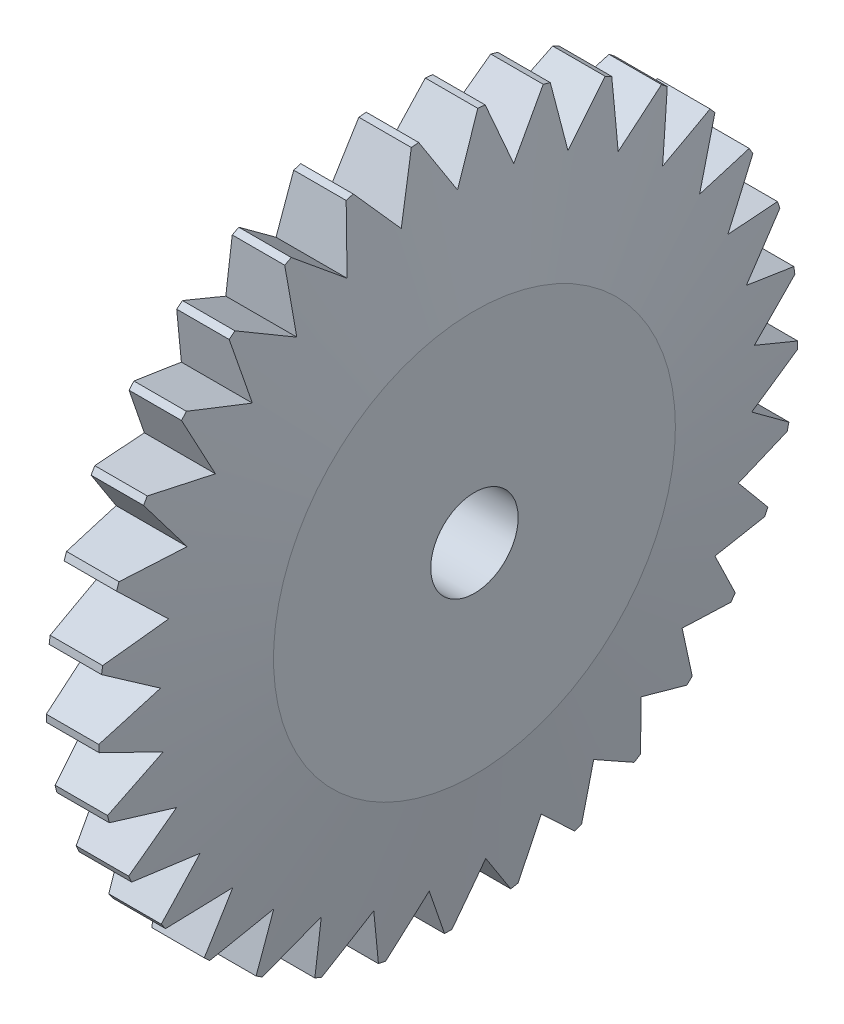
SolidWorks part; units mm, degrees
ref_plane "Front Plane" through (0, 0, 0) normal (0, 0, 1) x (1, 0, 0)
ref_plane "Top Plane" through (0, 0, 0) normal (0, 1, 0) x (1, 0, 0)
ref_plane "Right Plane" through (0, 0, 0) normal (1, 0, 0) x (0, 0, -1)
sketch "Sketch1" plane through (0, 0, 0) normal (1, 0, 0) x (0, 0, -1)
  circle A0 centre (0, 0) radius 40
  circle A1 centre (0, 0) radius 5
  dimension "D1" = 80
  dimension "D2" = 10
extrude "Boss-Extrude1" add sketch "Sketch1" along normal mid plane 12
sketch "Sketch2" plane through (6, 0, 0) normal (1, 0, 0) x (0, 0, -1)
  line L0 (0, 1.033) -> (0, 49.8392) construction
  line L1 (0, 40) -> (0, 34)
  line L2 (0, 34) -> (3.3814, 39.8568)
  line L4 (-3.3814, 39.8568) -> (0, 34)
  circle A0 centre (0, 0) radius 40 construction
  arc A1 (-3.3814, 39.8568) -> (3.3814, 39.8568) centre (0, 34) cw
  dimension "D1" = 30
  dimension "D2" = 30
  dimension "D3" = 6
chamfer "Chamfer2" distance 3 angle 80 1 edges at (6, 0, -40)
chamfer "Chamfer3" distance 3 angle 80 1 edges at (-6, 0, -40)
extrude "Cut-Extrude2" cut sketch "Sketch2" against normal blind 12 contours L2 A1 L4
pattern_circular "CirPattern2" count 33 over 360 about axis through (0, 0, 0) along (1, 0, 0) of "Cut-Extrude2"
